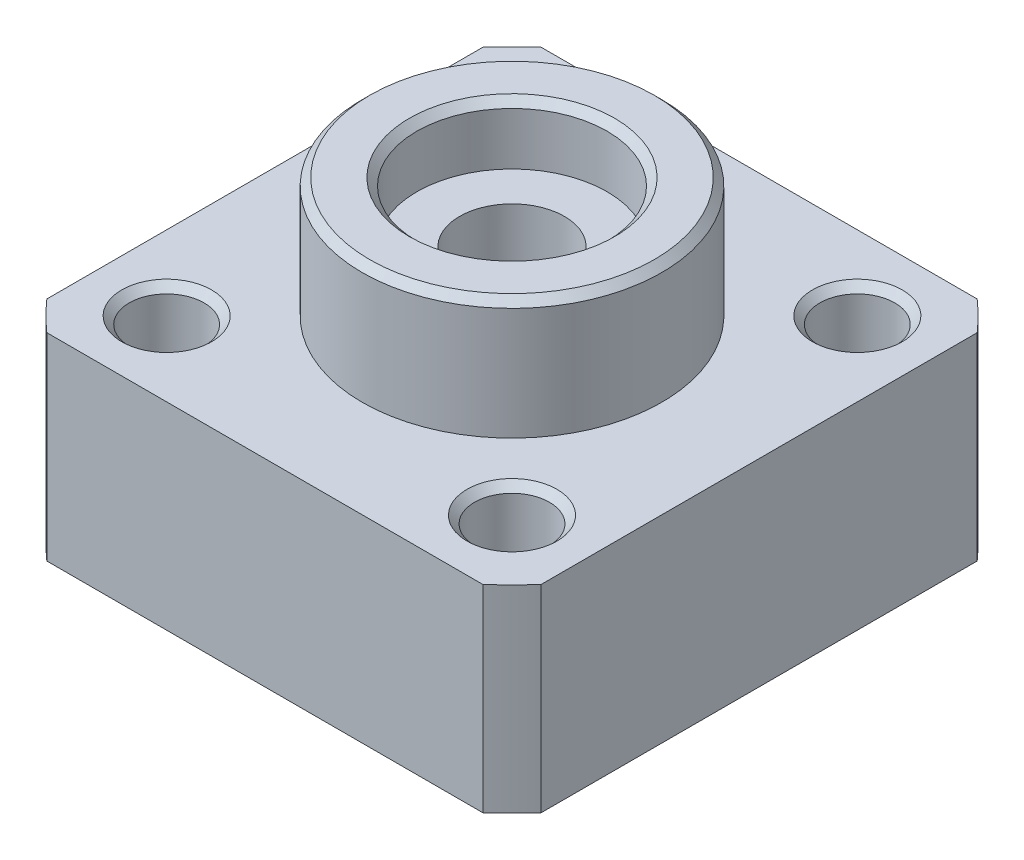
SolidWorks part; units mm, degrees
material "7075-T6 (SN)"
ref_plane "Front Plane" through (0, 0, 0) normal (0, 0, 1) x (1, 0, 0)
ref_plane "Top Plane" through (0, 0, 0) normal (0, 1, 0) x (1, 0, 0)
ref_plane "Right Plane" through (0, 0, 0) normal (1, 0, 0) x (0, 0, -1)
sketch "Sketch2" plane through (0, 0, 0) normal (0, 0, 1) x (1, 0, 0)
  line L0 (0, 0) -> (0, 42.1358) construction
  line L2 (-3.5, 0) -> (-22, 0)
  line L3 (-22, 0) -> (-22, 13.2)
  line L4 (-22, 13.2) -> (-10, 13.2)
  line L5 (-10, 13.2) -> (-10, 21.2)
  line L11 (-10, 21.2) -> (-6.35, 21.2)
  line L12 (-6.35, 21.2) -> (-6.35, 17.2)
  line L13 (-3.5, 17.2) -> (-3.5, 0)
  line L14 (-6.35, 17.2) -> (-3.5, 17.2)
  dimension "D1" = 44
  dimension "D2" = 13.2
  dimension "D3" = 12.7
  dimension "D4" = 20
  dimension "D5" = 8
  dimension "D6" = 7
  dimension "D7" = 4
revolve "Revolve1" add sketch "Sketch2" angle 360 about L0
sketch "Sketch3" plane through (0, 0, 0) normal (0, -1, 0) x (1, 0, 0)
  line L0 (-16.5, -16.5) -> (16.5, 16.5) construction
  line L1 (-16.5, 16.5) -> (16.5, 16.5)
  line L2 (-16.5, 16.5) -> (-16.5, -16.5)
  line L3 (-16.5, -16.5) -> (16.5, -16.5)
  line L4 (16.5, 16.5) -> (16.5, -16.5)
  line L5 (-29.5339, 27.809) -> (31.5533, 27.809)
  line L6 (-29.5339, 27.809) -> (-29.5339, -29.0711)
  line L7 (-29.5339, -29.0711) -> (31.5533, -29.0711)
  line L8 (31.5533, 27.809) -> (31.5533, -29.0711)
  dimension "D1" = 33
extrude "Cut-Extrude1" cut sketch "Sketch3" against normal through all
sketch "Sketch6" plane through (0, 0, 0) normal (0, -1, 0) x (1, 0, 0)
  line L0 (11.5258, 11.5258) -> (-11.5258, -11.5258) construction
  line L1 (-11.5258, 11.5258) -> (11.5258, 11.5258) construction
  line L2 (-11.5258, 11.5258) -> (-11.5258, -11.5258) construction
  line L3 (-11.5258, -11.5258) -> (11.5258, -11.5258) construction
  line L4 (11.5258, 11.5258) -> (11.5258, -11.5258) construction
  circle A0 centre (-11.5258, 11.5258) radius 2.5
  circle A1 centre (11.5258, 11.5258) radius 2.5
  circle A2 centre (-11.5258, -11.5258) radius 2.5
  circle A3 centre (11.5258, -11.5258) radius 2.5
  dimension "D2" = 5
  dimension "D1" = 32.6
extrude "Cut-Extrude5" cut sketch "Sketch6" against normal through all
sketch "Sketch5" plane through (0, 0, -16.5) normal (0, 0, -1) x (-1, 0, 0)
  line L0 (-14.5516, 13.2) -> (14.5516, 0) construction
  circle A0 centre (0, 6.6) radius 2
  circle A1 centre (0, 6.6) radius 4.25
  point P10 (0, 6.6)
  dimension "D1" = 4
  dimension "D2" = 8.5
extrude "Cut-Extrude3" cut sketch "Sketch5" against normal up to next contours A0 L0 | L0 A0
hole_wizard "G1/8 Tapped Hole1" positions "3DSketch1" profile "Sketch7" tap size "G1/8" standard "ISO"
sketch3d "3DSketch1"
  line L0 (0, 6.6, -2.8723) -> (0, 6.6, -16.5) construction
  point P0 (0, 6.6, -16.5)
cosmetic thread "Hole Thread1" parameters "D1"=10, "D2"=9.728
sketch "Sketch7" plane through (0, 6.6, -16.5) normal (1, 0, 0) x (0, 1, 0)
  line L0 (0, 0) -> (0, 12)
  line L1 (0, 12) -> (4.4, 9.3562)
  line L2 (4.4, 9.3562) -> (4.4, 0)
  line L5 (4.4, 0) -> (0, 0)
  line L10 (0, 12) -> (-4.4, 9.3562) construction
  line L11 (0, -6.35) -> (0, 107.95) construction
  dimension "Tap Drill Dia." = 8.8
  dimension "Tap Drill Depth" = 12
  dimension "Drill Angle" = 118
chamfer "Chamfer1" distance 0.5 angle 45 11 edges at (0, 21.2, -10) (0, 0, -3.5) (0, 21.2, -6.35) (-11.5258, 13.2, 9.0258) (-11.5258, 0, 9.0258) (-11.5258, 13.2, -14.0258) (-11.5258, 0, -14.0258) (11.5258, 13.2, -14.0258) (11.5258, 0, -14.0258) (11.5258, 13.2, 9.0258) (11.5258, 0, 9.0258)
